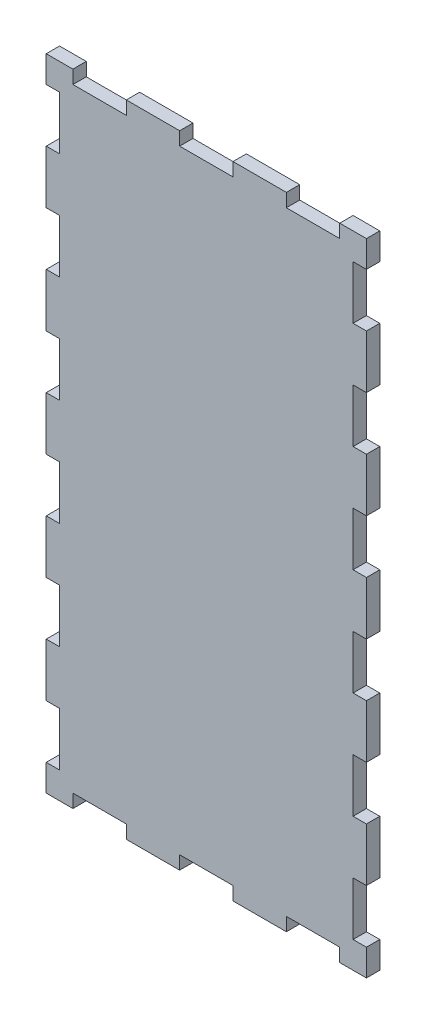
SolidWorks part; units mm, degrees
ref_plane "Front Plane" through (0, 0, 0) normal (0, 0, 1) x (1, 0, 0)
ref_plane "Top Plane" through (0, 0, 0) normal (0, 1, 0) x (1, 0, 0)
ref_plane "Right Plane" through (0, 0, 0) normal (1, 0, 0) x (0, 0, -1)
sketch "Sketch1" plane through (0, 0, 0) normal (0, 0, 1) x (1, 0, 0)
  line L1 (0, 0) -> (76.2, 0)
  line L2 (0, 0) -> (0, 152.4)
  line L3 (0, 152.4) -> (76.2, 152.4)
  line L4 (76.2, 0) -> (76.2, 152.4)
  dimension "D1" = 76.2
  dimension "D2" = 152.4
extrude "Extrude1" add sketch "Sketch1" along normal blind 3.175
sketch "Sketch3" plane through (0, 0, 3.175) normal (0, 0, 1) x (1, 0, 0)
  line L0 (76.2, 0) -> (76.2, 152.4) construction
  line L1 (76.2, 146.05) -> (73.025, 146.05)
  line L2 (76.2, 146.05) -> (76.2, 133.35)
  line L3 (76.2, 133.35) -> (73.025, 133.35)
  line L4 (73.025, 146.05) -> (73.025, 133.35)
  line L5 (76.2, 152.4) -> (0, 152.4) construction
  dimension "D1" = 3.175
  dimension "D2" = 12.7
  dimension "D3" = 6.35
extrude "Cut-Extrude1" cut sketch "Sketch3" against normal blind 3.175
pattern_linear "LPattern1" count 6 spacing 25.4 along (0, -1, 0) count 2 spacing 73.025 along (-1, 0, 0) of "Cut-Extrude1"
sketch "Sketch4" plane through (0, 0, 3.175) normal (0, 0, 1) x (1, 0, 0)
  line L0 (76.2, 152.4) -> (0, 152.4) construction
  line L1 (69.85, 152.4) -> (57.15, 152.4)
  line L2 (69.85, 152.4) -> (69.85, 149.225)
  line L3 (69.85, 149.225) -> (57.15, 149.225)
  line L4 (57.15, 152.4) -> (57.15, 149.225)
  dimension "D1" = 12.7
  dimension "D2" = 3.175
  dimension "D3" = 6.35
extrude "Cut-Extrude2" cut sketch "Sketch4" against normal blind 3.175
pattern_linear "LPattern2" count 3 spacing 25.4 along (-1, 0, 0) count 2 spacing 149.225 along (0, -1, 0) of "Cut-Extrude2"
